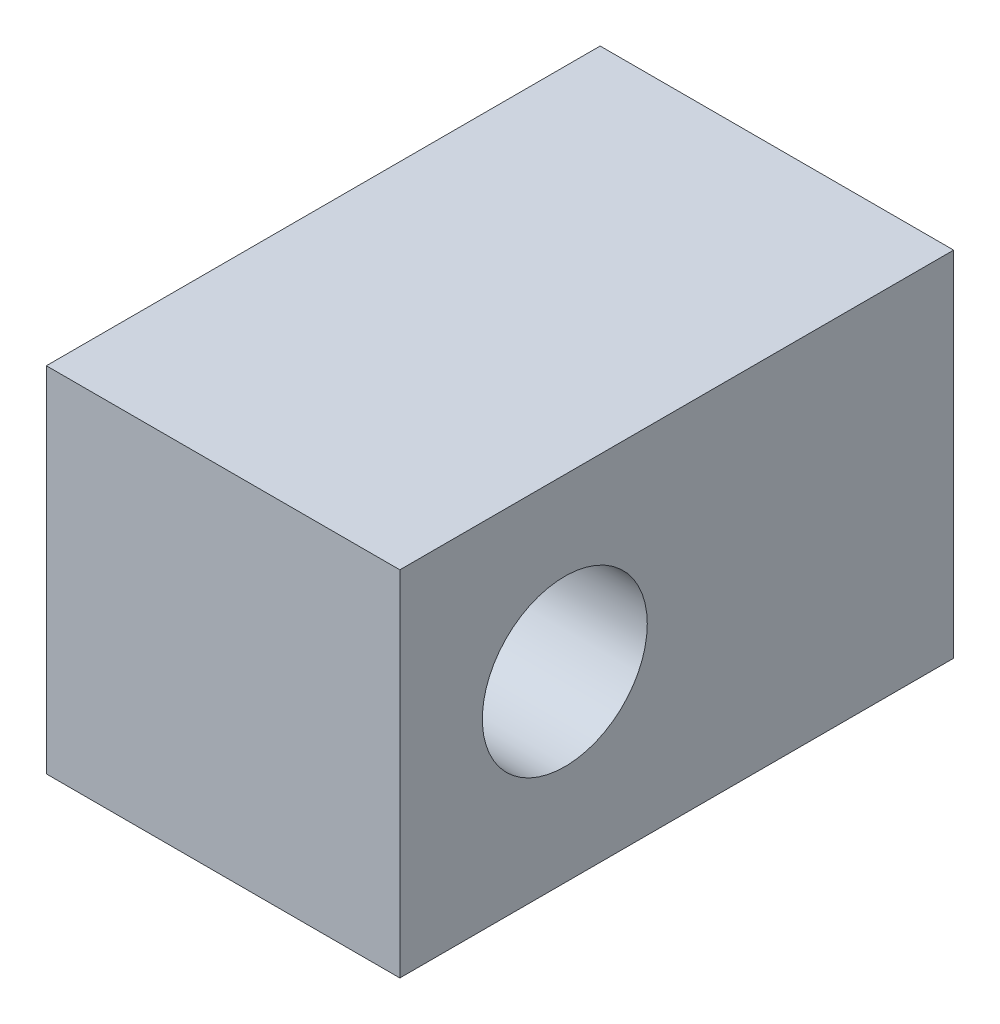
SolidWorks part; units mm, degrees
ref_plane "Front Plane" through (0, 0, 0) normal (0, 0, 1) x (1, 0, 0)
ref_plane "Top Plane" through (0, 0, 0) normal (0, 1, 0) x (1, 0, 0)
ref_plane "Right Plane" through (0, 0, 0) normal (1, 0, 0) x (0, 0, -1)
sketch "Sketch1" plane through (0, 0, 0) normal (0, 0, 1) x (1, 0, 0)
  line L1 (15, -15) -> (-15, -15)
  line L2 (15, -15) -> (15, 15)
  line L3 (15, 15) -> (-15, 15)
  line L4 (-15, -15) -> (-15, 15)
  line L5 (15, -15) -> (-15, 15) construction
  line L6 (15, 15) -> (-15, -15) construction
  point P0 (0, 0)
  dimension "D1" = 30
  dimension "D2" = 30
extrude "Boss-Extrude1" add sketch "Sketch1" along normal blind 47
sketch "Sketch2" plane through (15, 0, 0) normal (1, 0, 0) x (0, 0, -1)
  line L0 (-47, -15) -> (-47, 15) construction
  circle A0 centre (-33, 0.5258) radius 7
  dimension "D1" = 14
  dimension "D2" = 14
extrude "Cut-Extrude1" cut sketch "Sketch2" against normal blind 47
